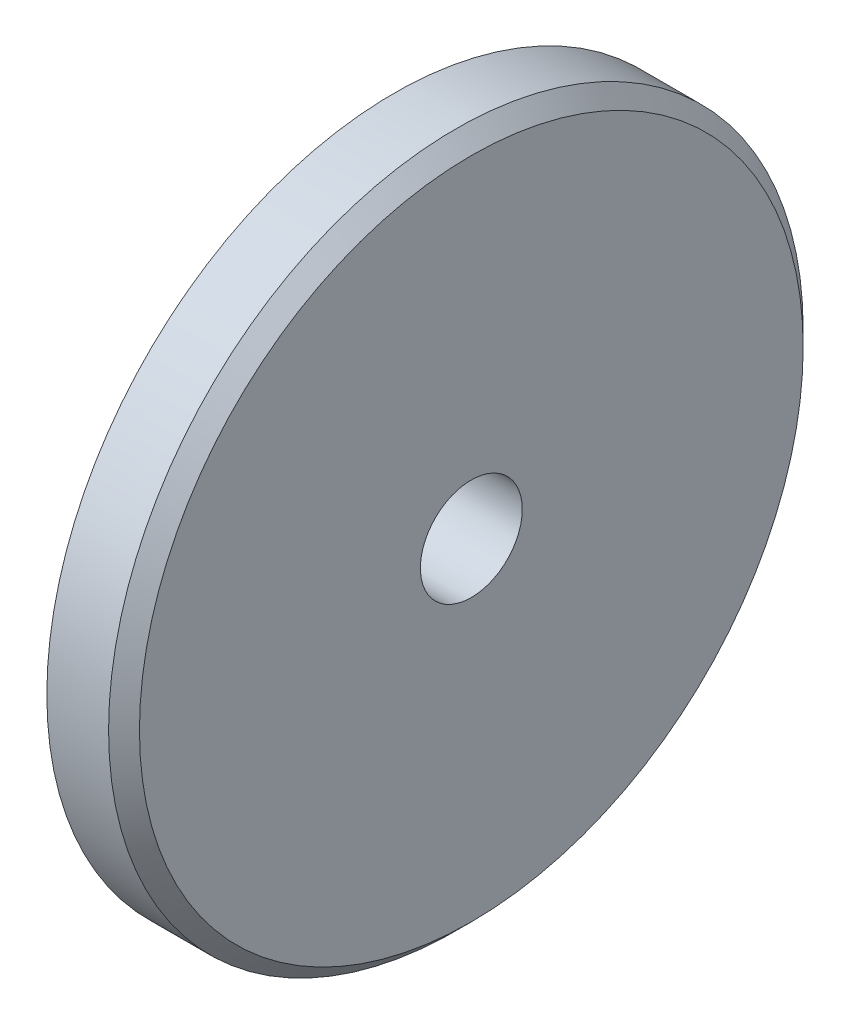
SolidWorks part; units mm, degrees
material "普通碳钢"
ref_plane "前视基准面" through (0, 0, 0) normal (0, 0, 1) x (1, 0, 0)
ref_plane "上视基准面" through (0, 0, 0) normal (0, 1, 0) x (1, 0, 0)
ref_plane "右视基准面" through (0, 0, 0) normal (1, 0, 0) x (0, 0, -1)
sketch "草图1" plane through (0, 0, 0) normal (1, 0, 0) x (0, 0, -1)
  circle A0 centre (0, 0) radius 3.3
  circle A1 centre (0, 0) radius 22.5
  dimension "D1" = 45
  dimension "D2" = 6.6
extrude "凸台-拉伸1" add sketch "草图1" along normal blind 5
chamfer "倒角1" distance 1 angle 45 1 edges at (5, 0, -22.5)
